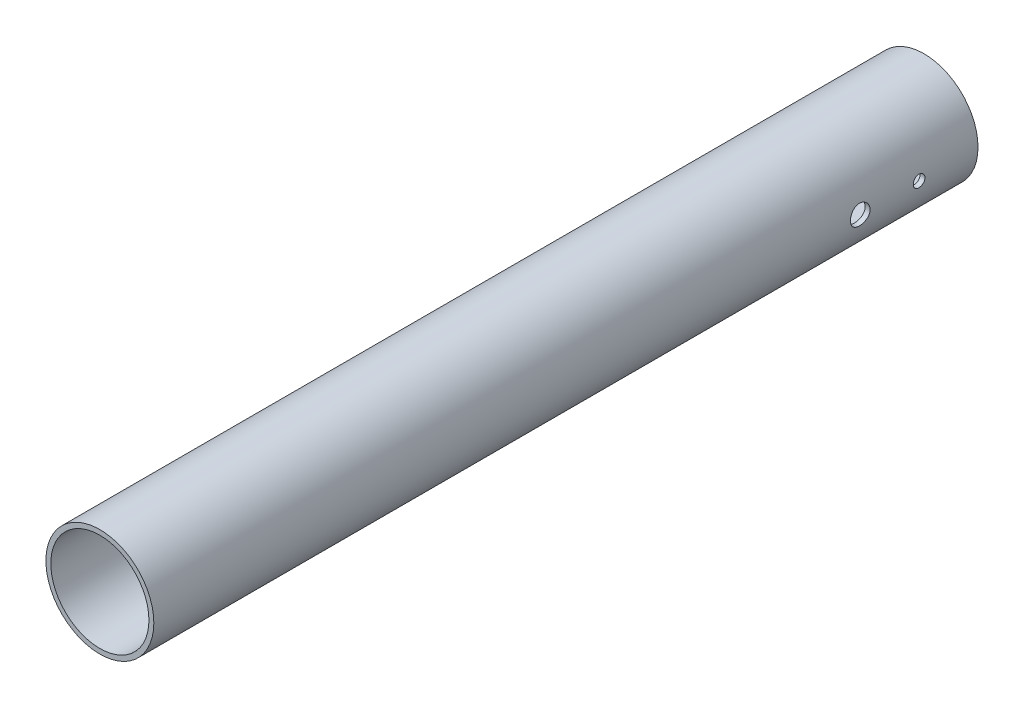
SolidWorks part; units mm, degrees
material "G-10"
ref_plane "Front Plane" through (0, 0, 0) normal (0, 0, 1) x (1, 0, 0)
ref_plane "Top Plane" through (0, 0, 0) normal (0, 1, 0) x (1, 0, 0)
ref_plane "Right Plane" through (0, 0, 0) normal (1, 0, 0) x (0, 0, -1)
sketch "Sketch2" plane through (0, 0, 0) normal (0, 0, 1) x (1, 0, 0)
  circle A0 centre (0, 0) radius 15.875
  circle A1 centre (0, 0) radius 17.4625
  dimension "D1" = 34.925
  dimension "D2" = 31.75
extrude "Boss-Extrude1" add sketch "Sketch2" along normal blind 266.7
hole_wizard "#6 Clearance Hole1" positions "3DSketch1" profile "Sketch3" hole size "#6" standard "ANSI Inch" end condition through all
sketch3d "3DSketch1"
  point P0 (17.4625, 0, 19.05)
  dimension "D1" = 19.05
sketch "Sketch3" plane through (17.4625, 0, 19.05) normal (0, 1, 0) x (0, 0, -1)
  line L0 (0, 0) -> (0, 34.925)
  line L1 (0, 34.925) -> (1.8986, 34.925)
  line L2 (1.8986, 34.925) -> (1.8986, 0)
  line L5 (1.8986, 0) -> (0, 0)
  line L11 (0, -6.35) -> (0, 107.95) construction
  dimension "Thru Hole Dia." = 3.7973
  dimension "Thru Hole Depth" = 34.925
hole_wizard "1/4 (0.25) Diameter Hole1" positions "3DSketch2" profile "Sketch4" hole size "1/4" standard "ANSI Inch"
sketch3d "3DSketch2"
  spline S0 degree 3 poles (17.4625, 0.2511, 17.1514) (17.4625, -0.1255, 17.1514) (17.4611, -0.249, 17.1637) (17.456, -0.4917, 17.212) (17.4521, -0.6124, 17.2485) (17.4426, -0.8422, 17.3438) (17.4369, -0.9513, 17.4022) (17.4244, -1.1576, 17.5399) (17.4176, -1.2552, 17.6201) (17.3973, -1.5177, 17.8826) (17.3838, -1.6591, 18.0943) (17.3646, -1.8486, 18.5511) (17.359, -1.8985, 18.8011) (17.359, -1.8987, 19.1729) (17.3603, -1.8864, 19.2988) (17.3655, -1.8379, 19.5423) (17.3693, -1.802, 19.6607) (17.3789, -1.7069, 19.8907) (17.3847, -1.6475, 20.0018) (17.3972, -1.5101, 20.2074) (17.4039, -1.4317, 20.3033) (17.4176, -1.2545, 20.4806) (17.4243, -1.1587, 20.5591) (17.4368, -0.9532, 20.6967) (17.4426, -0.8422, 20.7562) (17.4521, -0.6123, 20.8515) (17.4559, -0.494, 20.8875) (17.4611, -0.2506, 20.9361) (17.4625, -0.1247, 20.9486) (17.4625, 0.2472, 20.9487) (17.4569, 0.4972, 20.899) (17.4379, 0.9543, 20.7099) (17.4244, 1.1661, 20.5687) (17.4042, 1.4289, 20.3064) (17.3973, 1.5091, 20.2088) (17.3848, 1.647, 20.0027) (17.3791, 1.7054, 19.8937) (17.3695, 1.8009, 19.664) (17.3656, 1.8376, 19.5434) (17.3604, 1.8861, 19.3006) (17.359, 1.8985, 19.1773) (17.359, 1.8988, 18.9263) (17.3603, 1.8865, 18.8027) (17.3655, 1.8385, 18.5599) (17.3693, 1.8021, 18.4393) (17.3789, 1.7069, 18.2093) (17.3846, 1.6487, 18.1002) (17.3971, 1.5111, 17.8938) (17.404, 1.431, 17.7961) (17.4242, 1.1687, 17.5333) (17.4377, 0.9572, 17.3917) (17.4568, 0.5005, 17.2019) (17.4625, 0.2511, 17.1514) (17.4625, -0.1255, 17.1514) (17.4611, -0.249, 17.1637) knots -0.0625 -0.0625 0 0 0.03125 0.03125 0.0625 0.0625 0.09375 0.09375 0.125 0.125 0.1875 0.1875 0.25 0.25 0.28125 0.28125 0.3125 0.3125 0.34375 0.34375 0.375 0.375 0.40625 0.40625 0.4375 0.4375 0.46875 0.46875 0.5 0.5 0.5625 0.5625 0.625 0.625 0.65625 0.65625 0.6875 0.6875 0.71875 0.71875 0.75 0.75 0.78125 0.78125 0.8125 0.8125 0.84375 0.84375 0.875 0.875 0.9375 0.9375 1 1 1.03125 1.03125 1.0625 only from (17.4625, 0, 17.1514) to (17.4625, 0, 17.1514) construction
  spline S1 degree 3 poles (17.4625, 0.2511, 17.1514) (17.4625, -0.1255, 17.1514) (17.4611, -0.249, 17.1637) (17.456, -0.4917, 17.212) (17.4521, -0.6124, 17.2485) (17.4426, -0.8422, 17.3438) (17.4369, -0.9513, 17.4022) (17.4244, -1.1576, 17.5399) (17.4176, -1.2552, 17.6201) (17.3973, -1.5177, 17.8826) (17.3838, -1.6591, 18.0943) (17.3646, -1.8486, 18.5511) (17.359, -1.8985, 18.8011) (17.359, -1.8987, 19.1729) (17.3603, -1.8864, 19.2988) (17.3655, -1.8379, 19.5423) (17.3693, -1.802, 19.6607) (17.3789, -1.7069, 19.8907) (17.3847, -1.6475, 20.0018) (17.3972, -1.5101, 20.2074) (17.4039, -1.4317, 20.3033) (17.4176, -1.2545, 20.4806) (17.4243, -1.1587, 20.5591) (17.4368, -0.9532, 20.6967) (17.4426, -0.8422, 20.7562) (17.4521, -0.6123, 20.8515) (17.4559, -0.494, 20.8875) (17.4611, -0.2506, 20.9361) (17.4625, -0.1247, 20.9486) (17.4625, 0.2472, 20.9487) (17.4569, 0.4972, 20.899) (17.4379, 0.9543, 20.7099) (17.4244, 1.1661, 20.5687) (17.4042, 1.4289, 20.3064) (17.3973, 1.5091, 20.2088) (17.3848, 1.647, 20.0027) (17.3791, 1.7054, 19.8937) (17.3695, 1.8009, 19.664) (17.3656, 1.8376, 19.5434) (17.3604, 1.8861, 19.3006) (17.359, 1.8985, 19.1773) (17.359, 1.8988, 18.9263) (17.3603, 1.8865, 18.8027) (17.3655, 1.8385, 18.5599) (17.3693, 1.8021, 18.4393) (17.3789, 1.7069, 18.2093) (17.3846, 1.6487, 18.1002) (17.3971, 1.5111, 17.8938) (17.404, 1.431, 17.7961) (17.4242, 1.1687, 17.5333) (17.4377, 0.9572, 17.3917) (17.4568, 0.5005, 17.2019) (17.4625, 0.2511, 17.1514) (17.4625, -0.1255, 17.1514) (17.4611, -0.249, 17.1637) knots -0.0625 -0.0625 0 0 0.03125 0.03125 0.0625 0.0625 0.09375 0.09375 0.125 0.125 0.1875 0.1875 0.25 0.25 0.28125 0.28125 0.3125 0.3125 0.34375 0.34375 0.375 0.375 0.40625 0.40625 0.4375 0.4375 0.46875 0.46875 0.5 0.5 0.5625 0.5625 0.625 0.625 0.65625 0.65625 0.6875 0.6875 0.71875 0.71875 0.75 0.75 0.78125 0.78125 0.8125 0.8125 0.84375 0.84375 0.875 0.875 0.9375 0.9375 1 1 1.03125 1.03125 1.0625 only from (17.4625, 0, 17.1514) to (17.4625, 0, 17.1514)
  point P0 (17.4625, 0, 38.1)
  dimension "D1" = 38.1
sketch "Sketch4" plane through (17.4625, 0, 38.1) normal (0, 1, 0) x (0, 0, -1)
  line L0 (0, 0) -> (0, 1.5875)
  line L1 (0, 1.5875) -> (3.175, 1.5875)
  line L2 (3.175, 1.5875) -> (3.175, 0)
  line L5 (3.175, 0) -> (0, 0)
  line L11 (0, -6.35) -> (0, 107.95) construction
  dimension "Thru Hole Dia." = 6.35
  dimension "Thru Hole Depth" = 1.5875
